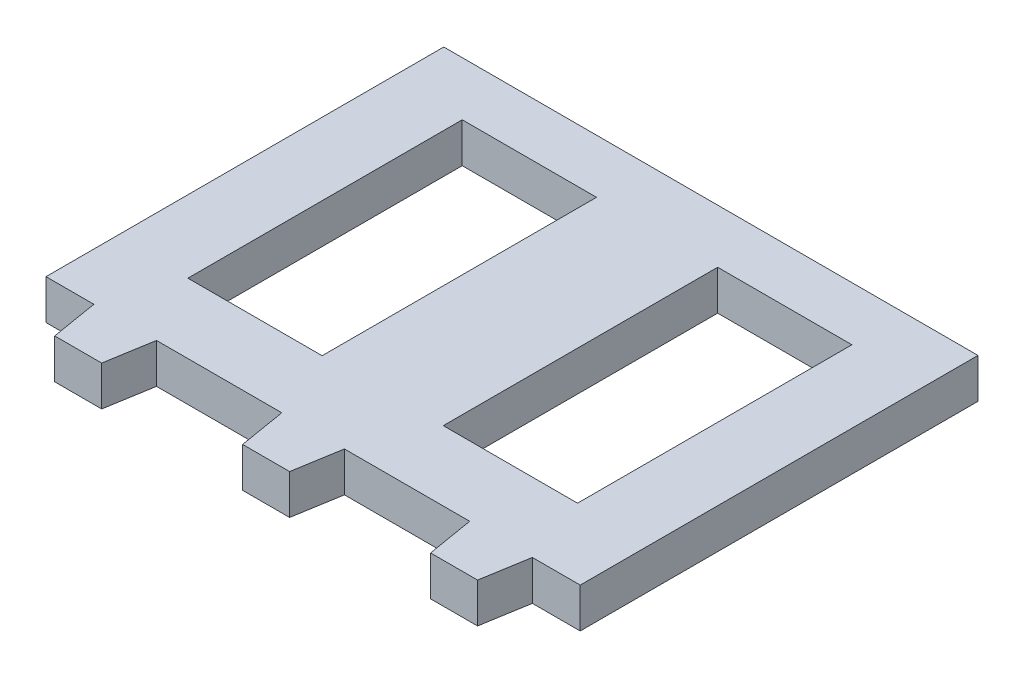
SolidWorks part; units mm, degrees
ref_plane "Front Plane" through (0, 0, 0) normal (0, 0, 1) x (1, 0, 0)
ref_plane "Top Plane" through (0, 0, 0) normal (0, 1, 0) x (1, 0, 0)
ref_plane "Right Plane" through (0, 0, 0) normal (1, 0, 0) x (0, 0, -1)
sketch "Sketch2" plane through (0, 0, 0) normal (0, 1, 0) x (1, 0, 0)
  line L0 (0, 0) -> (0, -127889.9036) construction
  line L1 (-42.6398, 31.75) -> (42.6398, 31.75)
  line L2 (-42.6398, 31.75) -> (-42.6398, -31.75)
  line L3 (-42.6398, -31.75) -> (42.6398, -31.75)
  line L4 (42.6398, 31.75) -> (42.6398, -31.75)
  line L5 (-42.6398, 31.75) -> (42.6398, -31.75) construction
  line L6 (-42.6398, -31.75) -> (42.6398, 31.75) construction
  line L7 (-5, -31.75) -> (5, -31.75)
  line L8 (5, -31.75) -> (3.75, -39.25)
  line L9 (3.75, -39.25) -> (-3.75, -39.25)
  line L10 (-3.75, -39.25) -> (-5, -31.75)
  line L11 (0, -31.75) -> (0, -96.5171) construction
  line L12 (-35, -31.75) -> (-25, -31.75)
  line L13 (-25, -31.75) -> (-26.25, -39.25)
  line L14 (-26.25, -39.25) -> (-33.75, -39.25)
  line L15 (-33.75, -39.25) -> (-35, -31.75)
  line L16 (-30, -31.75) -> (-30, -95.4613) construction
  line L21 (-60, -31.75) -> (-60, -90.4367) construction
  line L22 (60, -31.75) -> (60, -90.4367) construction
  line L23 (30, -31.75) -> (30, -95.4613) construction
  line L28 (33.75, -39.25) -> (35, -31.75)
  line L29 (26.25, -39.25) -> (33.75, -39.25)
  line L30 (25, -31.75) -> (26.25, -39.25)
  line L31 (35, -31.75) -> (25, -31.75)
  line L32 (31.1021, -20.6396) -> (9.6697, -20.6396)
  line L33 (-31.1021, 23.1589) -> (-9.6697, 23.1589)
  line L34 (-31.1021, 23.1589) -> (-31.1021, -20.6396)
  line L35 (-31.1021, -20.6396) -> (-9.6697, -20.6396)
  line L36 (-9.6697, 23.1589) -> (-9.6697, -20.6396)
  line L37 (9.6697, 23.1589) -> (9.6697, -20.6396)
  line L38 (31.1021, 23.1589) -> (9.6697, 23.1589)
  line L39 (31.1021, 23.1589) -> (31.1021, -20.6396)
  point P0 (0, 0)
  dimension "D1" = 10
  dimension "D2" = 7.5
  dimension "D3" = 7.5
  dimension "D5" = 10
  dimension "D6" = 7.5
  dimension "D7" = 7.5
  dimension "D8" = 3.75
  dimension "D13" = 20
extrude "Boss-Extrude1" add sketch "Sketch2" along normal blind 6.35
equation "\"toothBaseWidth\"=0.01"
equation "\"toothEndWidth\"=0.0075"
equation "\"toothLength\"=0.0075"
equation "\"D2@Sketch2\"= \"toothEndWidth\""
equation "\"D3@Sketch2\"= \"toothLength\""
equation "\"holeWidth\" = 0.009"
equation "\"motorHolderToothSeparation\" = 0.01"
equation "\"magnetHolderToothSeparation\" = 0.02"
equation "\"D13@Sketch2\"= \"magnetHolderToothSeparation\""
